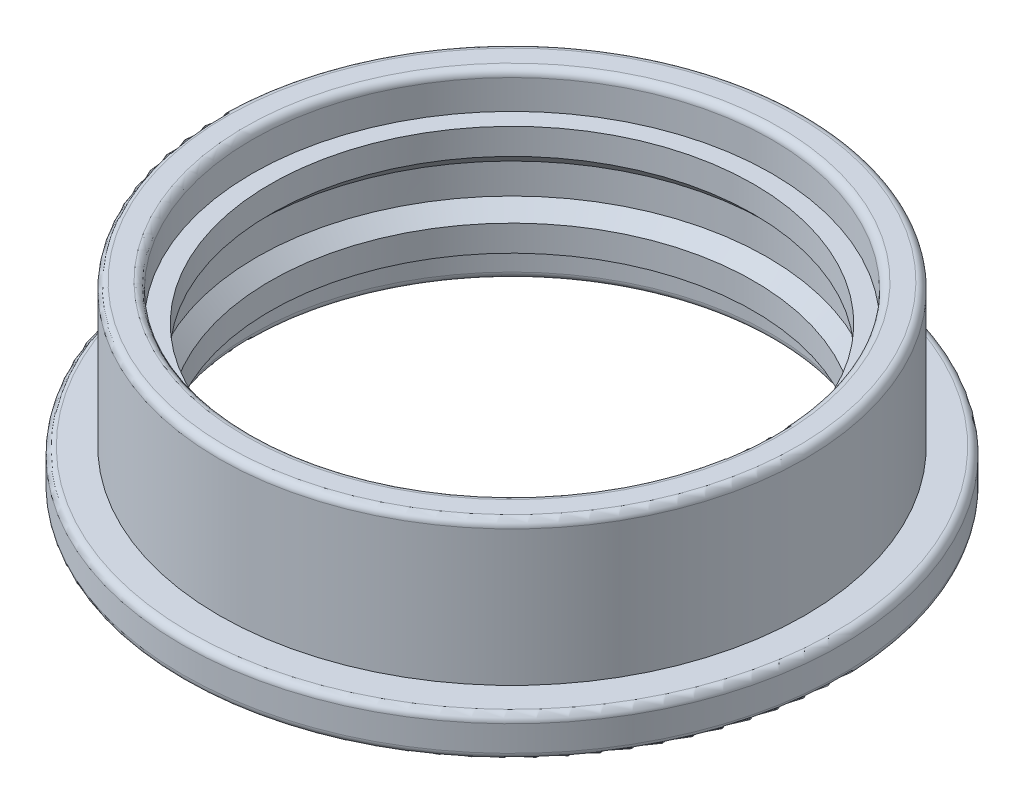
SolidWorks part; units mm, degrees
material "1060 Alloy"
ref_plane "Front" through (0, 0, 0) normal (0, 0, 1) x (1, 0, 0)
ref_plane "Top" through (0, 0, 0) normal (0, 1, 0) x (1, 0, 0)
ref_plane "Right" through (0, 0, 0) normal (1, 0, 0) x (0, 0, -1)
sketch "Çizim1" plane through (0, 0, 0) normal (0, 1, 0) x (1, 0, 0)
  circle A0 centre (0, 0) radius 6.6
  circle A1 centre (0, 0) radius 9
extrude "Yükseklik-Ekstrüzyon1" add sketch "Çizim1" along normal blind 5
sketch "Çizim2" plane through (0, 5, 0) normal (0, 1, 0) x (1, 0, 0)
  circle A0 centre (0, 0) radius 8
  circle A1 centre (0, 0) radius 9
extrude "Kes-Ekstrüzyon1" cut sketch "Çizim2" against normal blind 3.9
sketch "Çizim3" plane through (0, 5, 0) normal (0, 1, 0) x (1, 0, 0)
  circle A0 centre (0, 0) radius 7.1
extrude "Kes-Ekstrüzyon2" cut sketch "Çizim3" against normal blind 1
sketch "Çizim4" plane through (0, 0, 0) normal (0, 0, 1) x (1, 0, 0)
  line L0 (0, 0) -> (0, 5) construction
  line L1 (7.1, 5) -> (-7.1, 5) construction
pattern_linear "LÇoğaltma1" count 2 spacing 4 along (0, -1, 0) of "Kes-Ekstrüzyon2"
sketch "Çizim5" plane through (0, 0, 0) normal (0, 0, 1) x (1, 0, 0)
  line L0 (-6.975, 2.9142) -> (-6.975, 2.0858)
  line L3 (-6.975, 2.9142) -> (-5.8892, 4)
  line L4 (-6.975, 2.0858) -> (-5.8892, 1)
  line L6 (-5.8892, 4) -> (-5.8892, 1)
  line L8 (0, 0) -> (0, 5) construction
  line L9 (8, 5) -> (-8, 5) construction
revolve "Kes-Döndür1" cut sketch "Çizim5" angle 360 about L8
fillet "Radyus1" radius 0.2 5 edges at (0, 0, 7.1) (0, 0, 9) (0, 1.1, 9) (0, 5, 8) (0, 5, 7.1)
